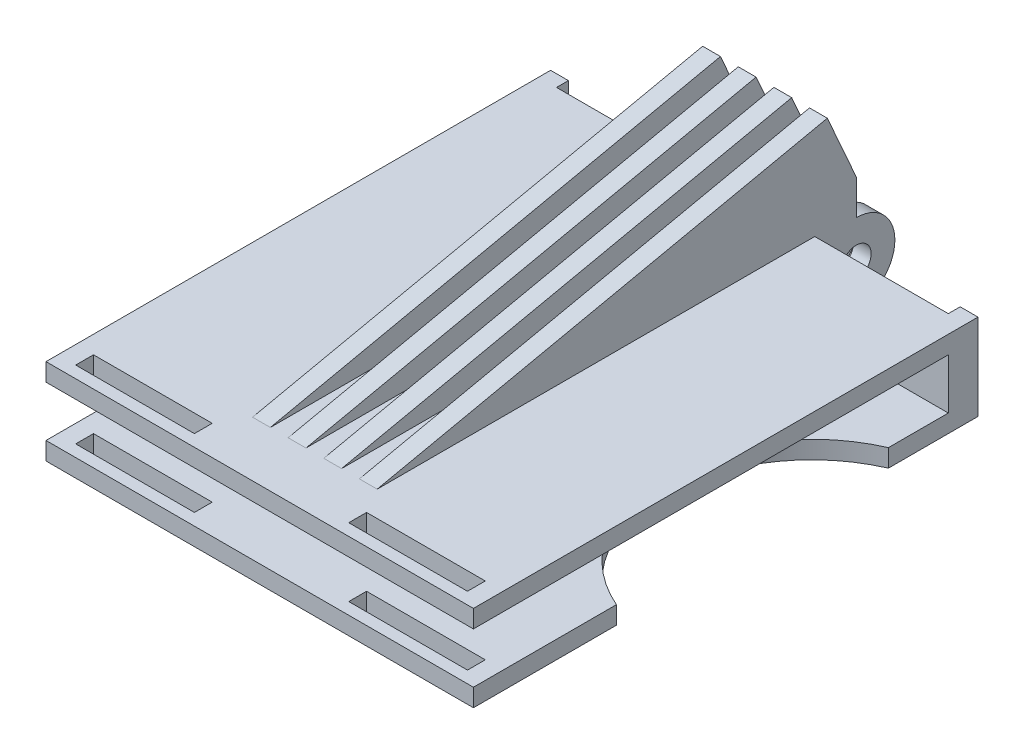
SolidWorks part; units mm, degrees
ref_plane "前视基准面" through (0, 0, 0) normal (0, 0, 1) x (1, 0, 0)
ref_plane "上视基准面" through (0, 0, 0) normal (0, 1, 0) x (1, 0, 0)
ref_plane "右视基准面" through (0, 0, 0) normal (1, 0, 0) x (0, 0, -1)
sketch "草图1" plane through (0, 0, 0) normal (0, 0, 1) x (1, 0, 0)
  line L0 (0, 0) -> (72, 0)
  line L1 (72, 0) -> (72, 14.5)
  line L2 (72, 14.5) -> (0, 14.5)
  line L3 (0, 14.5) -> (0, 0)
extrude "凸台-拉伸1" add sketch "草图1" along normal blind 3
sketch "草图2" plane through (0, 0, 3) normal (0, 0, 1) x (1, 0, 0)
  line L0 (0, 0) -> (0, 3)
  line L1 (0, 14.5) -> (0, 0) construction
  line L2 (0, 3) -> (72, 3)
  line L3 (72, 0) -> (72, 14.5) construction
  line L4 (72, 3) -> (72, 0)
  line L5 (72, 0) -> (0, 0)
  line L7 (72, 11.5) -> (72, 14.5)
  line L8 (72, 14.5) -> (0, 14.5)
  line L9 (0, 14.5) -> (0, 11.5)
  line L10 (0, 11.5) -> (72, 11.5)
extrude "凸台-拉伸2" add sketch "草图2" along normal blind 80
sketch "草图3" plane through (0, 0, 0) normal (0, 0, -1) x (-1, 0, 0)
  line L0 (-37.5, 13.75) -> (-37.5, 0.75)
  line L1 (-40.5, 0.75) -> (-37.5, 0.75)
  line L2 (-43.5, 0.75) -> (-43.5, 7.25)
  line L3 (-46.5, 0.75) -> (-43.5, 0.75)
  line L9 (-34.5, 13.75) -> (-34.5, 0.75)
  line L14 (-34.5, 13.75) -> (-31.5, 13.75)
  line L15 (-31.5, 13.75) -> (-31.5, 0.75)
  line L16 (-31.5, 0.75) -> (-34.5, 0.75)
  line L17 (-46.5, 13.75) -> (-46.5, 0.75)
  line L18 (-28.5, 7.25) -> (-28.5, 13.75)
  line L19 (-28.5, 13.75) -> (-25.5, 13.75)
  line L20 (-25.5, 13.75) -> (-25.5, 0.75)
  line L21 (-25.5, 0.75) -> (-28.5, 0.75)
  line L23 (-28.5, 0.75) -> (-28.5, 7.25)
  line L24 (-43.5, 13.75) -> (-46.5, 13.75)
  line L25 (-43.5, 7.25) -> (-43.5, 13.75)
  line L26 (-40.5, 13.75) -> (-40.5, 0.75)
  line L27 (-37.5, 13.75) -> (-40.5, 13.75)
extrude "凸台-拉伸3" add sketch "草图3" along normal blind 13.5
sketch "草图4" plane through (25.5, 0, 0) normal (-1, 0, 0) x (0, 0, 1)
  line L2 (-13.5, 13.75) -> (0, 13.75) construction
  line L3 (-13.5, 0.75) -> (0, 0.75) construction
  line L4 (-7, 0.75) -> (-7, -0.9327)
  line L5 (-7, -0.9327) -> (-15.1507, -0.9327)
  line L6 (-15.1507, -0.9327) -> (-15.1507, 14.8491)
  line L7 (-15.1507, 14.8491) -> (-7, 13.75)
  circle A0 centre (-7, 7.25) radius 2.5
  arc A1 (-7, 13.75) -> (-7, 0.75) centre (-7, 7.25) ccw
extrude "切除-拉伸1" cut sketch "草图4" against normal blind 21
sketch "草图5" plane through (0, 14.5, 0) normal (0, 1, 0) x (1, 0, 0)
  line L3 (3, -81) -> (23, -81)
  line L4 (23, -81) -> (23, -78)
  line L5 (23, -78) -> (3, -78)
  line L6 (3, -78) -> (3, -81)
  line L9 (49, -81) -> (49, -78)
  line L10 (69, -78) -> (69, -81)
  line L11 (69, -81) -> (49, -81)
  line L12 (49, -78) -> (69, -78)
extrude "切除-拉伸2" cut sketch "草图5" against normal blind 21
sketch "草图6" plane through (0, 0, 0) normal (0, 0, -1) x (-1, 0, 0)
  line L0 (-72, 14.5) -> (-69, 14.5)
  line L1 (-72, 14.5) -> (0, 14.5) construction
  line L7 (-69, 14.5) -> (-69, 0)
  line L12 (-69, 0) -> (-72, 0)
  line L13 (-72, 0) -> (-72, 14.5)
  line L15 (0, 0) -> (0, 14.5)
  line L16 (-3, 0) -> (0, 0)
  line L17 (-3, 14.5) -> (-3, 0)
  line L18 (0, 14.5) -> (-3, 14.5)
extrude "凸台-拉伸5" add sketch "草图6" along normal blind 2
sketch "草图8" plane through (0, 13.75, 0) normal (0, 1, 0) x (1, 0, 0)
  line L0 (25.5, 7) -> (28.5, 7)
  line L1 (25.5, 7) -> (25.5, -73.7083)
  line L2 (25.5, -73.7083) -> (28.5, -73.7083)
  line L3 (28.5, -73.7083) -> (28.5, 7)
  line L4 (31.5, 7) -> (34.5, 7)
  line L5 (34.5, 7) -> (34.5, -73.7083)
  line L6 (34.5, -73.7083) -> (31.5, -73.7083)
  line L7 (31.5, -73.7083) -> (31.5, 7)
  line L27 (37.5, -73.7083) -> (40.5, -73.7083)
  line L28 (37.5, 7) -> (37.5, -73.7083)
  line L29 (40.5, 7) -> (37.5, 7)
  line L30 (40.5, -73.7083) -> (40.5, 7)
  line L31 (43.5, -73.7083) -> (43.5, 7)
  line L32 (46.5, -73.7083) -> (43.5, -73.7083)
  line L33 (46.5, 7) -> (46.5, -73.7083)
  line L34 (46.5, 7) -> (43.5, 7)
extrude "凸台-拉伸6" add sketch "草图8" along normal blind 18
sketch "草图9" plane through (25.5, 0, 0) normal (-1, 0, 0) x (0, 0, 1)
  line L0 (-7, 31.75) -> (73.7083, 14.5)
  line L1 (73.7083, 14.5) -> (73.7083, 31.75)
  line L2 (73.7083, 31.75) -> (-7, 31.75)
extrude "切除-拉伸3" cut sketch "草图9" against normal blind 21
ref_plane "基准面4" through (72, 0, -2) normal (0, 0, -1) x (-1, 0, 0)
sketch "草图12" plane through (0, 0, 0) normal (0, -1, 0) x (1, 0, 0)
  circle A0 centre (82, 36) radius 25
extrude "切除-拉伸5" cut sketch "草图12" against normal blind 8
sketch "草图13" plane through (25.5, 0, 0) normal (-1, 0, 0) x (0, 0, 1)
  line L0 (-7, 19.6854) -> (-2.116, 30.7061)
  line L1 (-7, 31.75) -> (-7, 13.75) construction
  line L2 (-7, 31.75) -> (73.7083, 14.5) construction
  line L3 (-2.116, 30.7061) -> (-3.1413, 37.3491)
  line L4 (-3.1413, 37.3491) -> (-11.4983, 31.75)
  line L5 (-11.4983, 31.75) -> (-7, 19.6854)
extrude "切除-拉伸6" cut sketch "草图13" against normal blind 31
